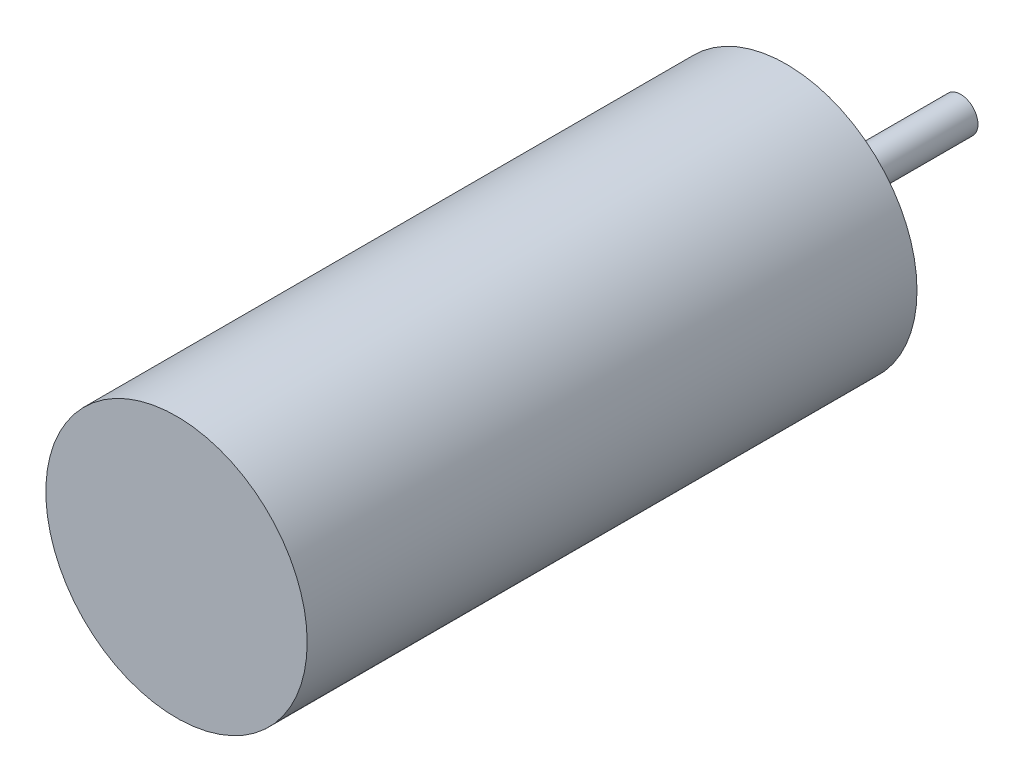
SolidWorks part; units mm, degrees
ref_plane "정면" through (0, 0, 0) normal (0, 0, 1) x (1, 0, 0)
ref_plane "윗면" through (0, 0, 0) normal (0, 1, 0) x (1, 0, 0)
ref_plane "우측면" through (0, 0, 0) normal (1, 0, 0) x (0, 0, -1)
sketch "스케치1" plane through (0, 0, 0) normal (0, 0, 1) x (1, 0, 0)
  circle A0 centre (0, 0) radius 3
  point P2 (0, 0)
  dimension "D1" = 6
extrude "보스-돌출1" add sketch "스케치1" along normal blind 14
sketch "스케치2" plane through (0, 0, 0) normal (0, 0, -1) x (-1, 0, 0)
  circle A0 centre (0, 0) radius 0.4
  dimension "D1" = 0.8
extrude "보스-돌출2" add sketch "스케치2" along normal blind 4
